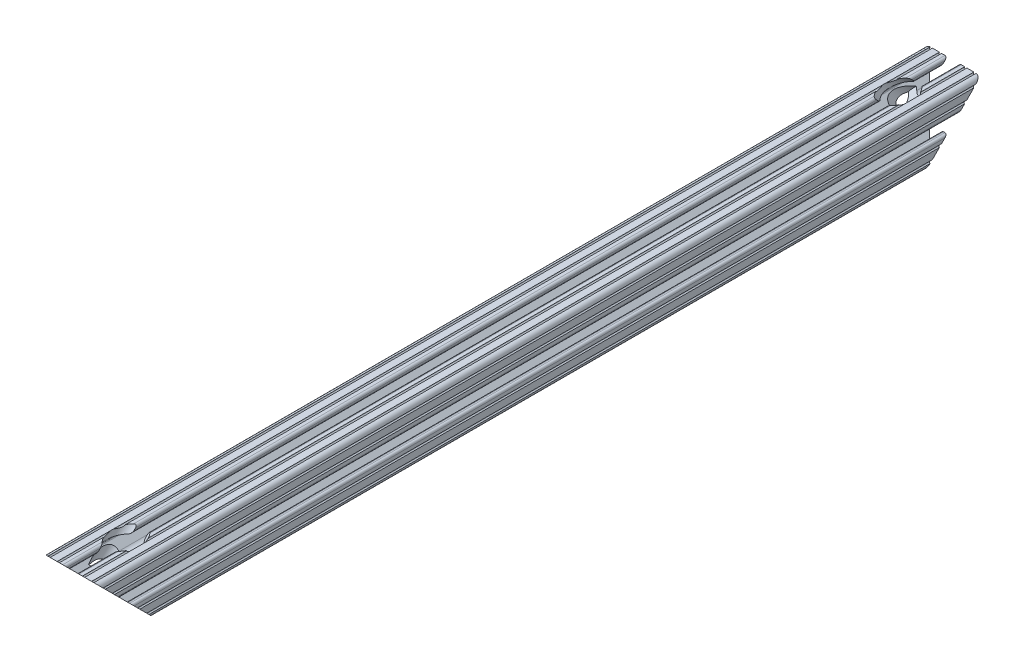
SolidWorks part; units mm, degrees
ref_plane "Front Plane" through (0, 0, 0) normal (0, 0, 1) x (1, 0, 0)
ref_plane "Top Plane" through (0, 0, 0) normal (0, 1, 0) x (1, 0, 0)
ref_plane "Right Plane" through (0, 0, 0) normal (1, 0, 0) x (0, 0, -1)
sketch "Sketch1" plane through (0, 0, 0) normal (0, 0, 1) x (1, 0, 0)
  line L2 (-10.287, 13.5524) -> (-10.287, 14.0843)
  line L3 (-9.3853, 14.986) -> (-5.6176, 14.986)
  line L4 (-4.064, 16.5396) -> (-4.064, 17.4964)
  line L6 (-5.6176, 19.05) -> (-7.9742, 19.05)
  line L7 (-9.4982, 19.05) -> (-14.3277, 19.05)
  line L8 (-19.05, 14.3277) -> (-19.05, 9.4961)
  line L9 (-19.05, 7.9763) -> (-19.05, 5.6176)
  line L10 (-17.4964, 4.064) -> (-16.5396, 4.064)
  line L11 (-14.986, 5.6176) -> (-14.986, 9.3853)
  line L12 (-14.0843, 10.287) -> (-13.516, 10.287)
  line L13 (-12.8784, 10.0229) -> (-8.1476, 5.2921)
  line L14 (-6.7564, 1.9335) -> (-6.7564, -1.9335)
  line L15 (-8.1476, -5.2921) -> (-12.8784, -10.0229)
  line L16 (-13.516, -10.287) -> (-14.0843, -10.287)
  line L17 (-14.986, -9.3853) -> (-14.986, -5.6176)
  line L18 (-16.5396, -4.064) -> (-17.4964, -4.064)
  line L19 (-19.05, -5.6176) -> (-19.05, -7.9763)
  line L20 (-19.05, -9.4961) -> (-19.05, -14.3277)
  line L21 (-14.3277, -19.05) -> (-9.4961, -19.05)
  line L22 (-7.9763, -19.05) -> (-5.6176, -19.05)
  line L23 (-4.064, -17.4964) -> (-4.064, -16.5396)
  line L24 (-5.6176, -14.986) -> (-9.3853, -14.986)
  line L25 (-10.287, -14.0843) -> (-10.287, -13.5524)
  line L26 (-10.0229, -12.9148) -> (-5.2522, -8.144)
  line L27 (-1.9022, -6.7564) -> (1.9022, -6.7564)
  line L28 (5.2522, -8.144) -> (10.0229, -12.9148)
  line L29 (10.287, -13.5524) -> (10.287, -14.0843)
  line L30 (9.3853, -14.986) -> (5.6176, -14.986)
  line L31 (4.064, -16.5396) -> (4.064, -17.4964)
  line L32 (5.6176, -19.05) -> (7.9763, -19.05)
  line L33 (9.4961, -19.05) -> (14.3277, -19.05)
  line L34 (19.05, -14.3277) -> (19.05, -9.4961)
  line L35 (19.05, -7.9763) -> (19.05, -5.6176)
  line L36 (17.4964, -4.064) -> (16.5396, -4.064)
  line L37 (14.986, -5.6176) -> (14.986, -9.3853)
  line L38 (14.0843, -10.287) -> (13.516, -10.287)
  line L39 (12.8784, -10.0229) -> (8.1476, -5.2921)
  line L40 (6.7564, -1.9335) -> (6.7564, 1.9335)
  line L41 (8.1476, 5.2921) -> (12.8784, 10.0229)
  line L42 (13.516, 10.287) -> (14.0843, 10.287)
  line L43 (14.986, 9.3853) -> (14.986, 5.6176)
  line L44 (16.5396, 4.064) -> (17.4964, 4.064)
  line L45 (19.05, 5.6176) -> (19.05, 7.9763)
  line L46 (19.05, 9.4961) -> (19.05, 14.3277)
  line L47 (14.3277, 19.05) -> (9.4982, 19.05)
  line L48 (7.9742, 19.05) -> (5.6176, 19.05)
  line L49 (4.064, 17.4964) -> (4.064, 16.5396)
  line L50 (5.6176, 14.986) -> (9.3853, 14.986)
  line L51 (10.287, 14.0843) -> (10.287, 13.5524)
  line L52 (10.0229, 12.9148) -> (5.2522, 8.144)
  line L53 (1.9022, 6.7564) -> (-1.9022, 6.7564)
  line L54 (-5.2522, 8.144) -> (-10.0229, 12.9148)
  circle A0 centre (0, 0) radius 3.3274
  arc A1 (-9.3853, 14.986) -> (-10.287, 14.0843) centre (-9.3853, 14.0843) ccw
  arc A2 (-5.6176, 14.986) -> (-4.064, 16.5396) centre (-5.6176, 16.5396) ccw
  arc A3 (-4.064, 17.4964) -> (-5.6176, 19.05) centre (-5.6176, 17.4964) ccw
  arc A4 (-9.4982, 19.05) -> (-7.9742, 19.05) centre (-8.7362, 19.05) ccw
  arc A5 (-15.8475, 19.05) -> (-14.3277, 19.05) centre (-15.0876, 18.9933) ccw
  arc A6 (-15.8475, 19.05) -> (-19.05, 15.8475) centre (-15.8751, 15.8751) ccw
  arc A7 (-19.05, 14.3277) -> (-19.05, 15.8475) centre (-18.9933, 15.0876) ccw
  arc A8 (-19.05, 7.9763) -> (-19.05, 9.4961) centre (-18.9933, 8.7362) ccw
  arc A9 (-19.05, 5.6176) -> (-17.4964, 4.064) centre (-17.4964, 5.6176) ccw
  arc A10 (-16.5396, 4.064) -> (-14.986, 5.6176) centre (-16.5396, 5.6176) ccw
  arc A11 (-14.0843, 10.287) -> (-14.986, 9.3853) centre (-14.0843, 9.3853) ccw
  arc A12 (-12.8784, 10.0229) -> (-13.516, 10.287) centre (-13.516, 9.3853) ccw
  arc A13 (-6.7564, 1.9335) -> (-8.1476, 5.2921) centre (-11.5062, 1.9335) ccw
  arc A14 (-8.1476, -5.2921) -> (-6.7564, -1.9335) centre (-11.5062, -1.9335) ccw
  arc A15 (-13.516, -10.287) -> (-12.8784, -10.0229) centre (-13.516, -9.3853) ccw
  arc A16 (-14.986, -9.3853) -> (-14.0843, -10.287) centre (-14.0843, -9.3853) ccw
  arc A17 (-14.986, -5.6176) -> (-16.5396, -4.064) centre (-16.5396, -5.6176) ccw
  arc A18 (-17.4964, -4.064) -> (-19.05, -5.6176) centre (-17.4964, -5.6176) ccw
  arc A19 (-19.05, -9.4961) -> (-19.05, -7.9763) centre (-18.9933, -8.7362) ccw
  arc A20 (-19.05, -15.8475) -> (-19.05, -14.3277) centre (-18.9933, -15.0876) ccw
  arc A21 (-19.05, -15.8475) -> (-15.8475, -19.05) centre (-15.8751, -15.8751) ccw
  arc A22 (-14.3277, -19.05) -> (-15.8475, -19.05) centre (-15.0876, -18.9933) ccw
  arc A23 (-7.9763, -19.05) -> (-9.4961, -19.05) centre (-8.7362, -18.9933) ccw
  arc A24 (-5.6176, -19.05) -> (-4.064, -17.4964) centre (-5.6176, -17.4964) ccw
  arc A25 (-4.064, -16.5396) -> (-5.6176, -14.986) centre (-5.6176, -16.5396) ccw
  arc A26 (-10.287, -14.0843) -> (-9.3853, -14.986) centre (-9.3853, -14.0843) ccw
  arc A27 (-10.0229, -12.9148) -> (-10.287, -13.5524) centre (-9.3853, -13.5524) ccw
  arc A28 (-1.9022, -6.7564) -> (-5.2522, -8.144) centre (-1.9022, -11.494) ccw
  arc A29 (5.2522, -8.144) -> (1.9022, -6.7564) centre (1.9022, -11.494) ccw
  arc A30 (10.287, -13.5524) -> (10.0229, -12.9148) centre (9.3853, -13.5524) ccw
  arc A31 (9.3853, -14.986) -> (10.287, -14.0843) centre (9.3853, -14.0843) ccw
  arc A32 (5.6176, -14.986) -> (4.064, -16.5396) centre (5.6176, -16.5396) ccw
  arc A33 (4.064, -17.4964) -> (5.6176, -19.05) centre (5.6176, -17.4964) ccw
  arc A34 (9.4961, -19.05) -> (7.9763, -19.05) centre (8.7362, -18.9933) ccw
  arc A35 (15.8475, -19.05) -> (14.3277, -19.05) centre (15.0876, -18.9933) ccw
  arc A36 (15.8475, -19.05) -> (19.05, -15.8475) centre (15.8751, -15.8751) ccw
  arc A37 (19.05, -14.3277) -> (19.05, -15.8475) centre (18.9933, -15.0876) ccw
  arc A38 (19.05, -7.9763) -> (19.05, -9.4961) centre (18.9933, -8.7362) ccw
  arc A39 (19.05, -5.6176) -> (17.4964, -4.064) centre (17.4964, -5.6176) ccw
  arc A40 (16.5396, -4.064) -> (14.986, -5.6176) centre (16.5396, -5.6176) ccw
  arc A41 (14.0843, -10.287) -> (14.986, -9.3853) centre (14.0843, -9.3853) ccw
  arc A42 (12.8784, -10.0229) -> (13.516, -10.287) centre (13.516, -9.3853) ccw
  arc A43 (6.7564, -1.9335) -> (8.1476, -5.2921) centre (11.5062, -1.9335) ccw
  arc A44 (8.1476, 5.2921) -> (6.7564, 1.9335) centre (11.5062, 1.9335) ccw
  arc A45 (13.516, 10.287) -> (12.8784, 10.0229) centre (13.516, 9.3853) ccw
  arc A46 (14.986, 9.3853) -> (14.0843, 10.287) centre (14.0843, 9.3853) ccw
  arc A47 (14.986, 5.6176) -> (16.5396, 4.064) centre (16.5396, 5.6176) ccw
  arc A48 (17.4964, 4.064) -> (19.05, 5.6176) centre (17.4964, 5.6176) ccw
  arc A49 (19.05, 9.4961) -> (19.05, 7.9763) centre (18.9933, 8.7362) ccw
  arc A50 (19.05, 15.8475) -> (19.05, 14.3277) centre (18.9933, 15.0876) ccw
  arc A51 (19.05, 15.8475) -> (15.8475, 19.05) centre (15.8751, 15.8751) ccw
  arc A52 (14.3277, 19.05) -> (15.8475, 19.05) centre (15.0876, 18.9933) ccw
  arc A53 (7.9742, 19.05) -> (9.4982, 19.05) centre (8.7362, 19.05) ccw
  arc A54 (5.6176, 19.05) -> (4.064, 17.4964) centre (5.6176, 17.4964) ccw
  arc A55 (4.064, 16.5396) -> (5.6176, 14.986) centre (5.6176, 16.5396) ccw
  arc A56 (10.287, 14.0843) -> (9.3853, 14.986) centre (9.3853, 14.0843) ccw
  arc A57 (10.0229, 12.9148) -> (10.287, 13.5524) centre (9.3853, 13.5524) ccw
  arc A58 (1.9022, 6.7564) -> (5.2522, 8.144) centre (1.9022, 11.494) ccw
  arc A59 (-5.2522, 8.144) -> (-1.9022, 6.7564) centre (-1.9022, 11.494) ccw
  arc A60 (-10.287, 13.5524) -> (-10.0229, 12.9148) centre (-9.3853, 13.5524) ccw
extrude "Boss-Extrude1" add sketch "Sketch1" along normal mid plane 609.6
sketch "Sketch2" plane through (0, 0, 0) normal (1, 0, 0) x (0, 0, -1)
  line L0 (-304.8, 19.05) -> (-304.8, -25.4)
  line L1 (-304.8, -25.4) -> (-260.35, -25.4)
  line L2 (-260.35, -25.4) -> (-304.8, 19.05)
  line L3 (0, 0) -> (0, -25.4) construction
  line L5 (260.35, -25.4) -> (304.8, 19.05)
  line L6 (304.8, -25.4) -> (260.35, -25.4)
  line L7 (304.8, 19.05) -> (304.8, -25.4)
  dimension "D1" = 25.4
extrude "Cut-Extrude1" cut sketch "Sketch2" against normal through all and the other way through all
sketch "Sketch3" plane through (0, 0, 0) normal (1, 0, 0) x (0, 0, -1)
  line L0 (-259.9648, 25.7852) -> (-285.75, 0)
  line L1 (-285.75, 0) -> (-288.0579, 2.3079)
  line L2 (-288.0579, 2.3079) -> (-283.5678, 6.7981)
  line L3 (-283.5678, 6.7981) -> (-287.9951, 11.2253)
  line L4 (-287.9951, 11.2253) -> (-266.7, 32.5204)
  line L5 (-266.7, 32.5204) -> (-259.9648, 25.7852)
  line L6 (-285.75, 0) -> (-288.0579, -2.3079) construction
  line L7 (-260.35, -25.4) -> (-304.8, 19.05) construction
  line L8 (-289.0774, 3.3274) -> (-282.4226, -3.3274) construction
  line L9 (-274.5247, -2.2451) -> (-253.2296, 19.05) construction
  dimension "D1" = 6.5278
  dimension "D2" = 19.05
  dimension "D3" = 6.35
revolve "Cut-Revolve1" cut sketch "Sketch3" angle 360 mid plane about L6
mirror "Mirror1" about plane through (0, 0, 0) normal (0, 0, 1) of "Cut-Revolve1"
